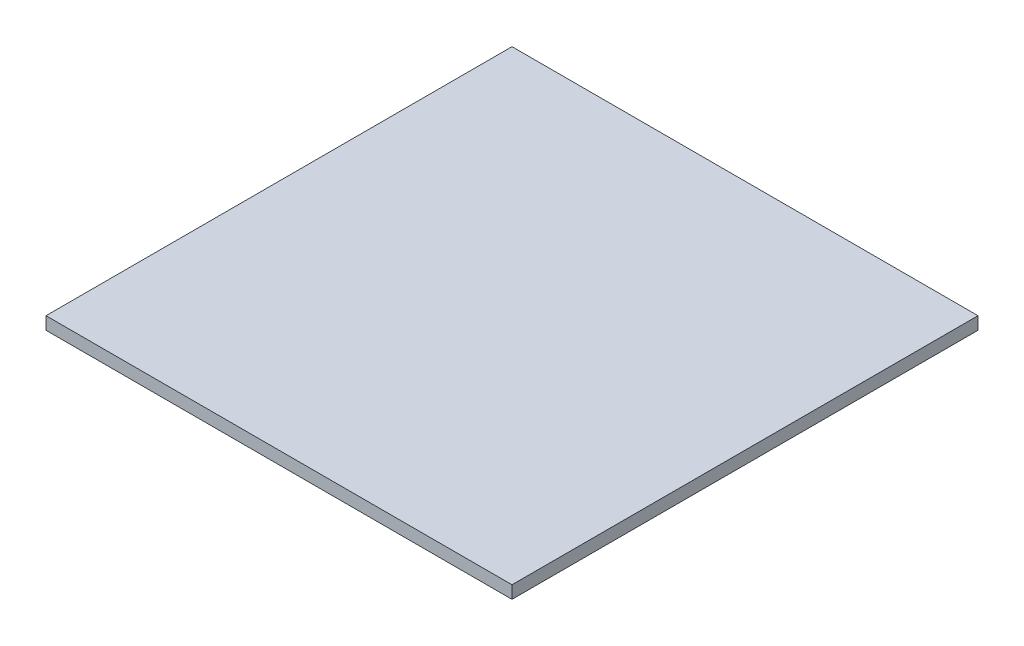
SolidWorks part; units mm, degrees
ref_plane "Alzado" through (0, 0, 0) normal (0, 0, 1) x (1, 0, 0)
ref_plane "Planta" through (0, 0, 0) normal (0, 1, 0) x (1, 0, 0)
ref_plane "Vista lateral" through (0, 0, 0) normal (1, 0, 0) x (0, 0, -1)
sketch "Croquis1" plane through (0, 0, 0) normal (0, 1, 0) x (1, 0, 0)
  line L1 (-35, 35) -> (35, 35)
  line L2 (-35, 35) -> (-35, -35)
  line L3 (-35, -35) -> (35, -35)
  line L4 (35, 35) -> (35, -35)
  line L5 (-35, 35) -> (35, -35) construction
  line L6 (-35, -35) -> (35, 35) construction
  point P0 (0, 0)
  dimension "D1" = 70
  dimension "D2" = 70
extrude "Saliente-Extruir1" add sketch "Croquis1" along normal blind 1.9
